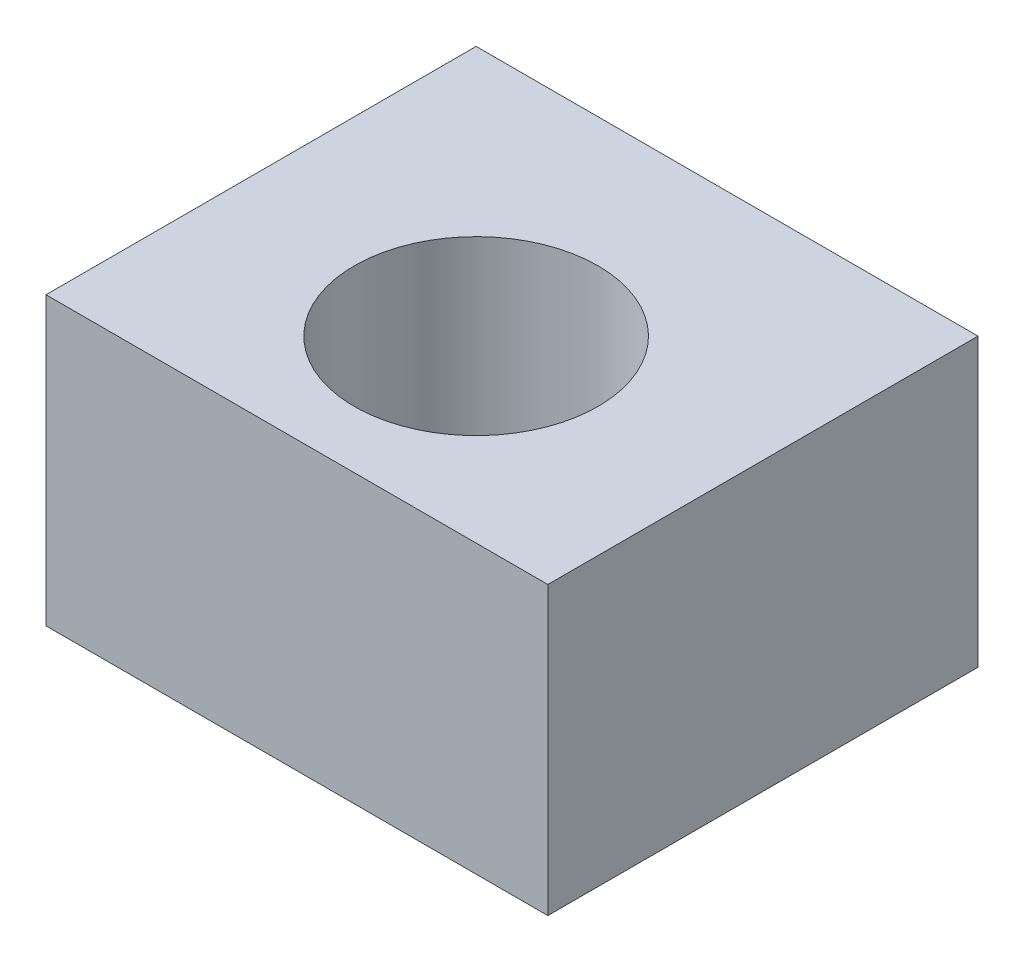
SolidWorks part; units mm, degrees
material "1060 Alloy"
ref_plane "Front Plane" through (0, 0, 0) normal (0, 0, 1) x (1, 0, 0)
ref_plane "Top Plane" through (0, 0, 0) normal (0, 1, 0) x (1, 0, 0)
ref_plane "Right Plane" through (0, 0, 0) normal (1, 0, 0) x (0, 0, -1)
sketch "Sketch1" plane through (0, 0, 0) normal (0, 1, 0) x (1, 0, 0)
  line L1 (-17.5, -17.5) -> (17.5, -17.5)
  line L2 (-17.5, -17.5) -> (-17.5, 17.5)
  line L3 (-17.5, 17.5) -> (17.5, 17.5)
  line L4 (17.5, -17.5) -> (17.5, 17.5)
  line L5 (-17.5, -17.5) -> (17.5, 17.5) construction
  line L6 (-17.5, 17.5) -> (17.5, -17.5) construction
  point P0 (0, 0)
  dimension "D1" = 35
  dimension "D2" = 35
extrude "Boss-Extrude1" add sketch "Sketch1" along normal blind 20
sketch "Sketch2" plane through (0, 20, 0) normal (0, 1, 0) x (1, 0, 0)
  line L0 (17.5, -17.5) -> (17.5, 17.5) construction
  line L1 (-17.5, 17.5) -> (17.5, 17.5)
  line L2 (-17.5, 17.5) -> (-17.5, 10.5)
  line L3 (-17.5, 10.5) -> (17.5, 10.5)
  line L4 (17.5, 17.5) -> (17.5, 10.5)
  dimension "D1" = 7
extrude "Boss-Extrude2" add sketch "Sketch2" along normal blind 27
sketch "Sketch3" plane through (0, 0, 0) normal (0, -1, 0) x (1, 0, 0)
  circle A0 centre (0, 0) radius 8.5
  dimension "D1" = 17
extrude "Cut-Extrude1" cut sketch "Sketch3" against normal blind 20
sketch "Sketch7" plane through (0, 20, 0) normal (0, 1, 0) x (1, 0, 0)
  line L0 (17.5, -17.5) -> (17.5, 10.5) construction
  line L1 (-17.5, -17.5) -> (17.5, -17.5)
  line L2 (-17.5, -17.5) -> (-17.5, -12.5)
  line L3 (-17.5, -12.5) -> (17.5, -12.5)
  line L4 (17.5, -17.5) -> (17.5, -12.5)
  dimension "D1" = 5
extrude "Cut-Extrude3" cut sketch "Sketch7" against normal up to next
sketch "Sketch9" plane through (-17.5, 0, 0) normal (-1, 0, 0) x (0, 0, 1)
  line L0 (-17.5, 47) -> (-10.5, 47) construction
  line L1 (-10.5, 20) -> (-17.5, 20)
  line L2 (-10.5, 20) -> (-10.5, 47)
  line L3 (-10.5, 47) -> (-17.5, 47)
  line L4 (-17.5, 20) -> (-17.5, 47)
extrude "Cut-Extrude4" cut sketch "Sketch9" against normal blind 40
hole_wizard "M3 Tapped Hole3" positions "Sketch10" profile "Sketch11" tap size "M3" standard "ISO"
sketch "Sketch10" plane through (0, 0, 0) normal (0, -1, 0) x (-1, 0, 0)
  line L0 (-17.5, -12.5) -> (17.5, -12.5) construction
  line L1 (17.5, 17.5) -> (17.5, -12.5) construction
  point P0 (12.5, 5.5)
  point P7 (-12.5, 5.5)
  point P9 (-12.5, -9.5)
  point P11 (12.5, -9.5)
  dimension "D1" = 25
  dimension "D2" = 15
  dimension "D3" = 3
  dimension "D4" = 5
sketch "Sketch11" plane through (-12.5, 0, -5.5) normal (1, 0, 0) x (0, 0, -1)
  line L0 (0, 0) -> (0, 8.2511)
  line L1 (0, 8.2511) -> (1.25, 7.5)
  line L2 (1.25, 7.5) -> (1.25, 0)
  line L5 (1.25, 0) -> (0, 0)
  line L10 (0, 8.2511) -> (-1.25, 7.5) construction
  line L11 (0, -6.35) -> (0, 107.95) construction
  dimension "Tap Drill Dia." = 2.5
  dimension "Tap Drill Depth" = 7.5
  dimension "Drill Angle" = 118
cosmetic thread "Hole Thread1" parameters "D1"=6, "D2"=3
cosmetic thread "Hole Thread2" parameters "D1"=6, "D2"=3
cosmetic thread "Hole Thread3" parameters "D1"=6, "D2"=3
cosmetic thread "Hole Thread4" parameters "D1"=6, "D2"=3
